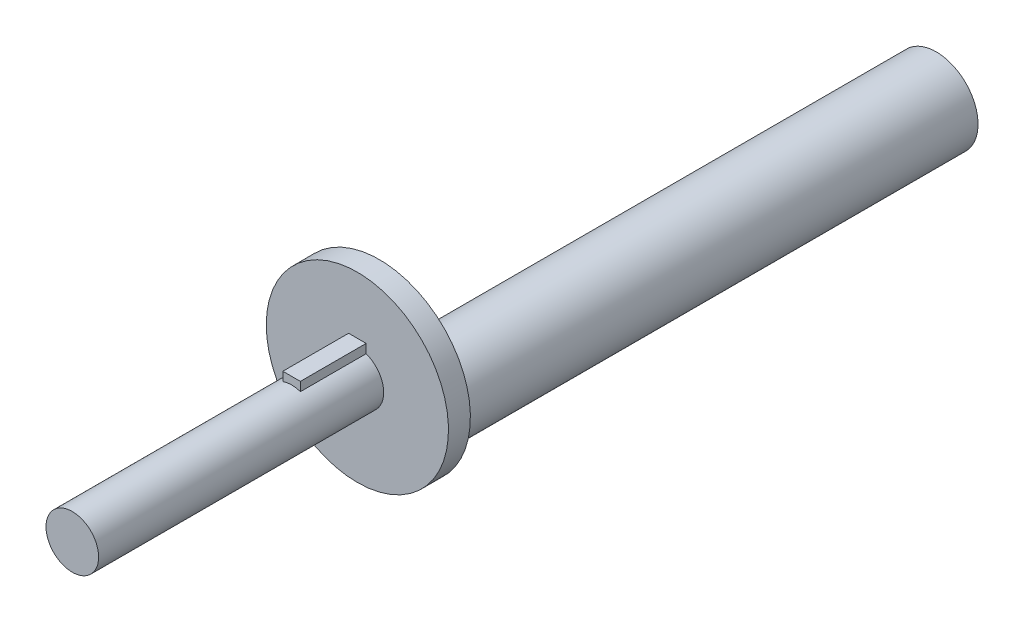
SolidWorks part; units mm, degrees
ref_plane "Front Plane" through (0, 0, 0) normal (0, 0, 1) x (1, 0, 0)
ref_plane "Top Plane" through (0, 0, 0) normal (0, 1, 0) x (1, 0, 0)
ref_plane "Right Plane" through (0, 0, 0) normal (1, 0, 0) x (0, 0, -1)
sketch "Sketch1" plane through (0, 0, 0) normal (0, 0, 1) x (1, 0, 0)
  line L0 (0, 0) -> (0, 7.7) construction
  line L1 (-2, 7.7) -> (2, 7.7)
  line L2 (2, 7.7) -> (2, 5.6569)
  line L4 (-2, 5.6569) -> (-2, 7.7)
  arc A0 (-2, 5.6569) -> (2, 5.6569) centre (0, 0) ccw
  point P4 (0, -6)
  point P7 (0, 7.7)
  dimension "D1" = 12
  dimension "D2" = 4
  dimension "D3" = 13.7
extrude "Boss-Extrude1" add sketch "Sketch1" along normal blind 15
sketch "Sketch2" plane through (0, 0, 0) normal (0, 0, -1) x (-1, 0, 0)
  circle A0 centre (0, 0) radius 20.775
  dimension "D1" = 41.55
extrude "Boss-Extrude2" add sketch "Sketch2" along normal blind 5
sketch "Sketch3" plane through (0, 0, -5) normal (0, 0, -1) x (-1, 0, 0)
  circle A2 centre (0, -11.25) radius 9.525
  point P2 (0, -26)
  dimension "D1" = 19.05
  dimension "D2" = 11.25
extrude "Boss-Extrude3" add sketch "Sketch3" along normal blind 127
sketch "Sketch4" plane through (0, 0, -132) normal (0, 0, -1) x (-1, 0, 0)
  line L0 (0.3333, -3.7794) -> (-2.4162, -108.5074)
  line L1 (14.6596, -16.8599) -> (7.6631, -3.9718)
  line L2 (7.6631, -3.9718) -> (-6.9965, -3.5869)
  line L3 (-6.9965, -3.5869) -> (-14.6596, -16.0901)
  line L4 (-14.6596, -16.0901) -> (-7.6631, -28.9782)
  line L5 (-7.6631, -28.9782) -> (6.9965, -29.3631)
  line L6 (6.9965, -29.3631) -> (14.6596, -16.8599)
  circle A0 centre (0, -16.475) radius 12.7 construction
  circle A1 centre (0, -11.25) radius 9.525
  circle A3 centre (0, -16.475) radius 92.0641
  circle A4 centre (0, -11.25) radius 9.525
  dimension "D2" = 25.4
  dimension "D1" = 0
sketch "Sketch6" plane through (0, 0, 15) normal (0, 0, 1) x (1, 0, 0)
  circle A0 centre (0, 0) radius 6
extrude "Boss-Extrude5" add sketch "Sketch6" along normal blind 50
